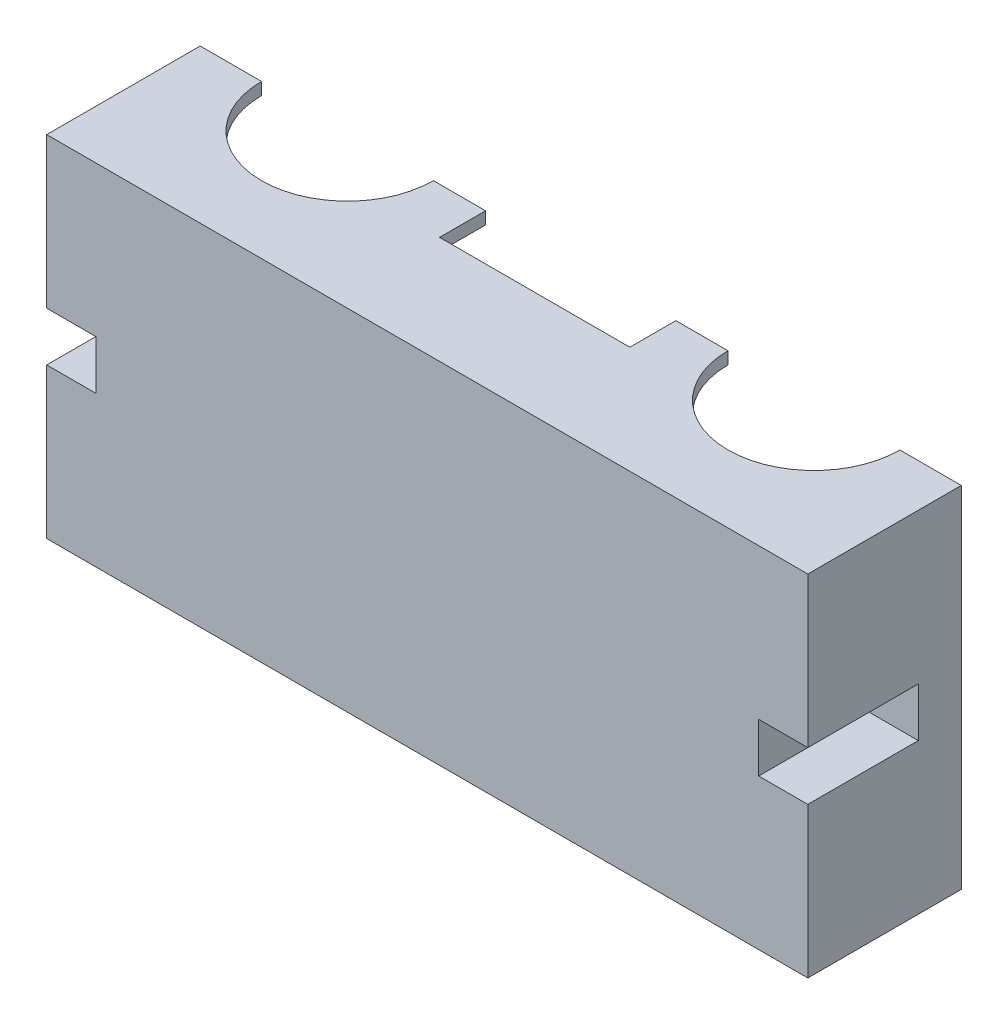
SolidWorks part; units mm, degrees
ref_plane "Ebene vorne" through (0, 0, 0) normal (0, 0, 1) x (1, 0, 0)
ref_plane "Ebene oben" through (0, 0, 0) normal (0, 1, 0) x (1, 0, 0)
ref_plane "Ebene rechts" through (0, 0, 0) normal (1, 0, 0) x (0, 0, -1)
sketch "Skizze1" plane through (0, 0, 0) normal (0, 0, 1) x (1, 0, 0)
  line L1 (-102.9591, -27.5852) -> (21.0409, -27.5852)
  line L2 (-102.9591, -27.5852) -> (-102.9591, 29.4148)
  line L3 (-102.9591, 29.4148) -> (21.0409, 29.4148)
  line L4 (21.0409, -27.5852) -> (21.0409, 29.4148)
  dimension "D1" = 124
  dimension "D2" = 57
extrude "Aufsatz-Linear austragen1" add sketch "Skizze1" along normal blind 25
sketch "Skizze2" plane through (0, 0, 25) normal (0, 0, 1) x (1, 0, 0)
  line L0 (21.0409, -27.5852) -> (21.0409, 29.4148) construction
  line L1 (21.0409, 4.9148) -> (13.0409, 4.9148)
  line L2 (21.0409, 4.9148) -> (21.0409, -3.0852)
  line L3 (21.0409, -3.0852) -> (13.0409, -3.0852)
  line L4 (13.0409, 4.9148) -> (13.0409, -3.0852)
  line L5 (21.0409, 29.4148) -> (-102.9591, 29.4148) construction
  line L7 (-102.9591, -27.5852) -> (21.0409, -27.5852) construction
  line L8 (-94.9591, 4.9148) -> (-102.9591, 4.9148)
  line L9 (-94.9591, 4.9148) -> (-94.9591, -3.0852)
  line L10 (-94.9591, -3.0852) -> (-102.9591, -3.0852)
  line L11 (-102.9591, 4.9148) -> (-102.9591, -3.0852)
  line L12 (-102.9591, 29.4148) -> (-102.9591, -27.5852) construction
  dimension "D1" = 8
  dimension "D2" = 8
  dimension "D3" = 24.5
  dimension "D4" = 24.5
  dimension "D5" = 0
  dimension "D6" = 24.5
  dimension "D7" = 24.5
  dimension "D8" = 8
  dimension "D9" = 8
extrude "Schnitt-Linear austragen4" cut sketch "Skizze2" against normal blind 18
sketch "Skizze5" plane through (0, 0, 0) normal (0, 0, -1) x (-1, 0, 0)
  line L0 (-21.0409, 29.4148) -> (102.9591, 29.4148) construction
  line L1 (-19.0409, 27.4148) -> (100.9591, 27.4148)
  line L2 (-19.0409, 27.4148) -> (-19.0409, 7.4148)
  line L3 (-19.0409, 7.4148) -> (100.9591, 7.4148)
  line L4 (100.9591, 27.4148) -> (100.9591, 7.4148)
  line L5 (-21.0409, -27.5852) -> (-21.0409, 29.4148) construction
  line L6 (102.9591, 29.4148) -> (102.9591, -27.5852) construction
  line L7 (-19.0409, -5.5852) -> (100.9591, -5.5852)
  line L8 (-19.0409, -5.5852) -> (-19.0409, -25.5852)
  line L9 (-19.0409, -25.5852) -> (100.9591, -25.5852)
  line L10 (100.9591, -5.5852) -> (100.9591, -25.5852)
  line L11 (102.9591, -27.5852) -> (-21.0409, -27.5852) construction
  line L13 (-11.5409, 7.4148) -> (93.4591, 7.4148)
  line L14 (-11.5409, 7.4148) -> (-11.5409, -5.5852)
  line L15 (-11.5409, -5.5852) -> (93.4591, -5.5852)
  line L16 (93.4591, 7.4148) -> (93.4591, -5.5852)
  dimension "D1" = 2
  dimension "D2" = 2
  dimension "D3" = 2
  dimension "D4" = 20
  dimension "D5" = 2
  dimension "D6" = 2
  dimension "D7" = 2
  dimension "D8" = 20
  dimension "D9" = 13
  dimension "D10" = 9.5
  dimension "D11" = 9.5
extrude "Schnitt-Linear austragen5" cut sketch "Skizze5" against normal blind 23 contours L4 L1 L2 L3 | L16 L3 L14 L7 | L10 L7 L8 L9
sketch "Skizze6" plane through (0, 29.4148, 0) normal (0, 1, 0) x (1, 0, 0)
  line L0 (21.0409, 0) -> (-102.9591, 0) construction
  line L1 (21.0409, -25) -> (21.0409, 0) construction
  line L2 (-102.9591, -25) -> (-102.9591, 0) construction
  line L4 (-25.4591, 0) -> (-56.4591, 0)
  line L5 (-25.4591, 0) -> (-25.4591, -7.5)
  line L6 (-25.4591, -7.5) -> (-56.4591, -7.5)
  line L7 (-56.4591, 0) -> (-56.4591, -7.5)
  circle A0 centre (-2.9591, 0) radius 14
  circle A1 centre (-78.9591, 0) radius 14
  dimension "D1" = 24
  dimension "D2" = 0
  dimension "D3" = 24
  dimension "D4" = 31
  dimension "D5" = 7.5
  dimension "D6" = 22.5
  dimension "D7" = 22.5
extrude "Schnitt-Linear austragen6" cut sketch "Skizze6" against normal blind 2
